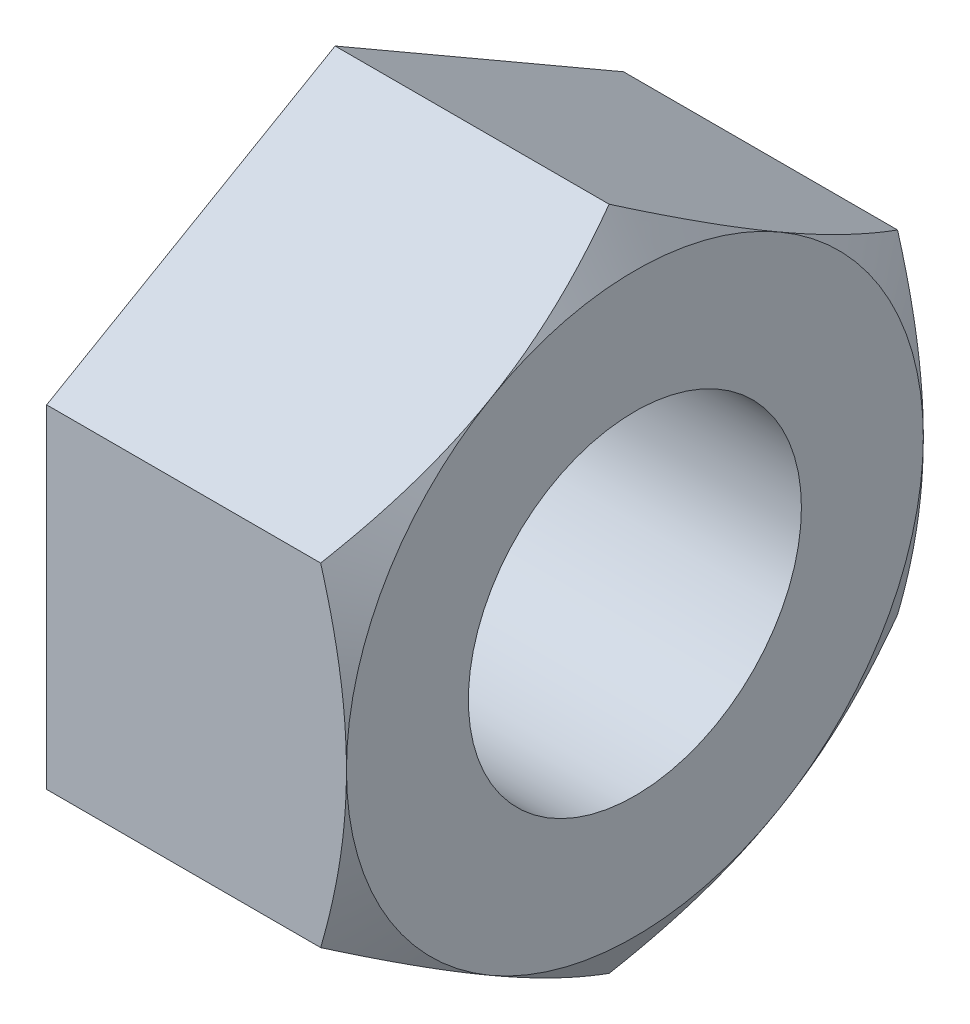
SolidWorks part; units mm, degrees
ref_plane "Front Plane" through (0, 0, 0) normal (0, 0, 1) x (1, 0, 0)
ref_plane "Top Plane" through (0, 0, 0) normal (0, 1, 0) x (1, 0, 0)
ref_plane "Right Plane" through (0, 0, 0) normal (1, 0, 0) x (0, 0, -1)
sketch "Sketch1" plane through (0, 0, 0) normal (1, 0, 0) x (0, 0, -1)
  line L1 (0, 28) -> (-24.2487, 14)
  line L2 (-24.2487, 14) -> (-24.2487, -14)
  line L3 (-24.2487, -14) -> (0, -28)
  line L4 (0, -28) -> (24.2487, -14)
  line L5 (24.2487, -14) -> (24.2487, 14)
  line L6 (24.2487, 14) -> (0, 28)
  dimension "D1" = 28
extrude "Boss-Extrude1" add sketch "Sketch1" against normal blind 25.2
sketch "Sketch2" plane through (0, 0, 0) normal (1, 0, 0) x (0, 0, -1)
  circle A0 centre (0, 0) radius 14
extrude "Cut-Extrude1" cut sketch "Sketch2" against normal blind 25.2
cosmetic thread "Cosmetic Thread1" parameters "D2"=33
sketch "Sketch3" plane through (0, 0, 0) normal (1, 0, 0) x (0, 0, -1)
  circle A0 centre (0, 0) radius 24.2487
extrude "Cut-Extrude2" cut sketch "Sketch3" against normal blind 25.2 draft 60 flip side to cut
